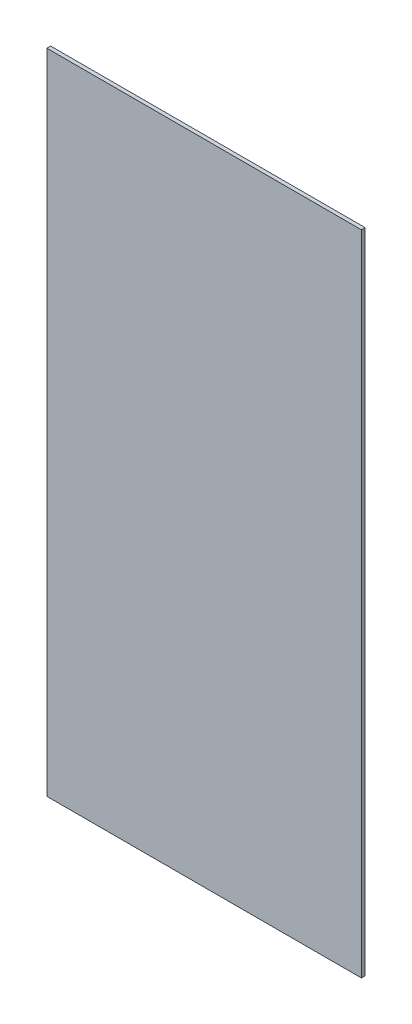
SolidWorks part; units mm, degrees
ref_plane "Přední rovina" through (0, 0, 0) normal (0, 0, 1) x (1, 0, 0)
ref_plane "Horní rovina" through (0, 0, 0) normal (0, 1, 0) x (1, 0, 0)
ref_plane "Pravá rovina" through (0, 0, 0) normal (1, 0, 0) x (0, 0, -1)
sketch "Skica1" plane through (0, 0, 0) normal (0, 0, 1) x (1, 0, 0)
  line L1 (-126.25, 260) -> (126.25, 260)
  line L2 (-126.25, 260) -> (-126.25, -260)
  line L3 (-126.25, -260) -> (126.25, -260)
  line L4 (126.25, 260) -> (126.25, -260)
  line L5 (-126.25, 260) -> (126.25, -260) construction
  line L6 (-126.25, -260) -> (126.25, 260) construction
  point P0 (0, 0)
  dimension "D1" = 252.5
  dimension "D2" = 520
extrude "Přidat vysunutím1" add sketch "Skica1" along normal blind 3
